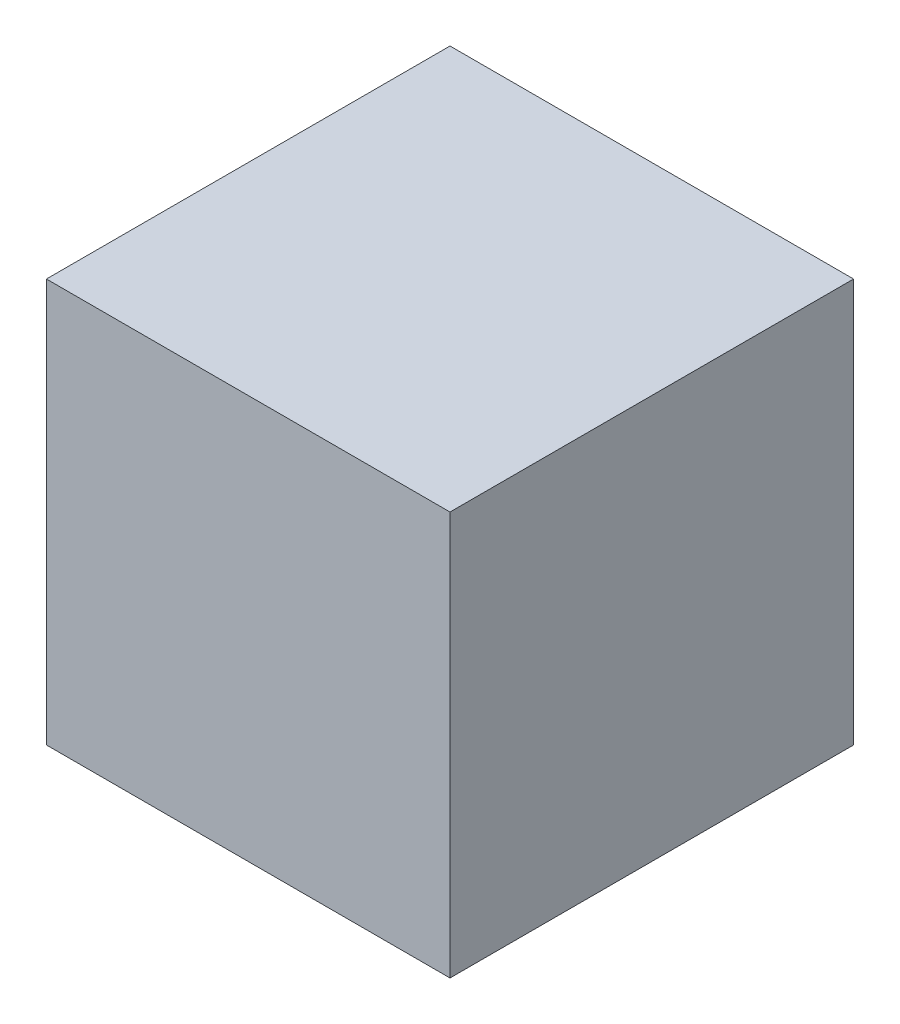
SolidWorks part; units mm, degrees
material "3.3315 (EN-AW 5005A)"
ref_plane "Ebene vorne" through (0, 0, 0) normal (0, 0, 1) x (1, 0, 0)
ref_plane "Ebene oben" through (0, 0, 0) normal (0, 1, 0) x (1, 0, 0)
ref_plane "Ebene rechts" through (0, 0, 0) normal (1, 0, 0) x (0, 0, -1)
sketch "Skizze1" plane through (0, 0, 0) normal (0, 0, 1) x (1, 0, 0)
  line L1 (-12.5, -12.5) -> (12.5, -12.5)
  line L2 (-12.5, -12.5) -> (-12.5, 12.5)
  line L3 (-12.5, 12.5) -> (12.5, 12.5)
  line L4 (12.5, -12.5) -> (12.5, 12.5)
  line L5 (0, 12.5) -> (0, -12.5) construction
  line L6 (-12.5, 0) -> (12.5, 0) construction
  point P0 (0, 0)
  dimension "D1" = 25
extrude "Aufsatz-Linear austragen1" add sketch "Skizze1" along normal mid plane 25
